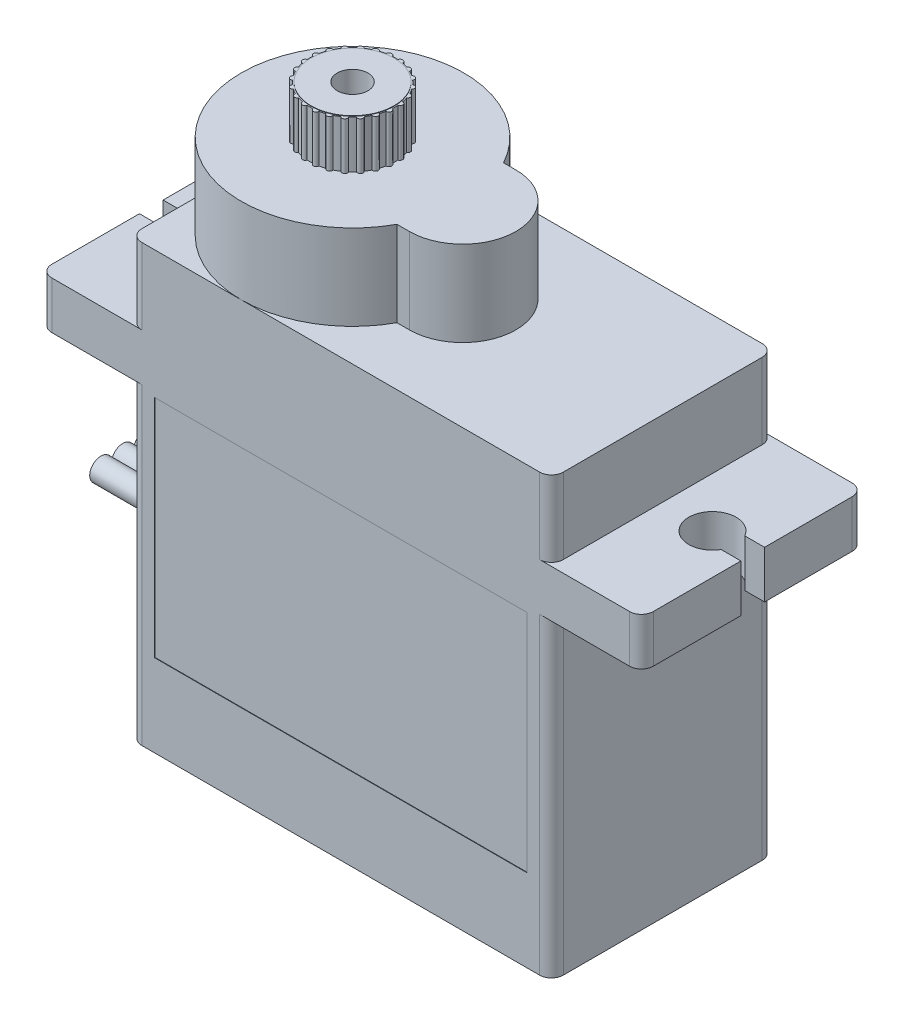
SolidWorks part; units mm, degrees
ref_plane "Front Plane" through (0, 0, 0) normal (0, 0, 1) x (1, 0, 0)
ref_plane "Top Plane" through (0, 0, 0) normal (0, 1, 0) x (1, 0, 0)
ref_plane "Right Plane" through (0, 0, 0) normal (1, 0, 0) x (0, 0, -1)
sketch "Sketch1" plane through (0, 0, 0) normal (0, 1, 0) x (1, 0, 0)
  line L1 (-11.303, -5.969) -> (11.303, -5.969)
  line L2 (-11.303, -5.969) -> (-11.303, 5.969)
  line L3 (-11.303, 5.969) -> (11.303, 5.969)
  line L4 (11.303, -5.969) -> (11.303, 5.969)
  line L5 (-11.303, -5.969) -> (11.303, 5.969) construction
  line L6 (-11.303, 5.969) -> (11.303, -5.969) construction
  point P0 (0, 0)
  dimension "D1" = 11.938
  dimension "D2" = 22.606
extrude "Boss-Extrude1" add sketch "Sketch1" along normal blind 23.368
sketch "Sketch3" plane through (0, 0, 0) normal (1, 0, 0) x (0, 0, -1)
  line L0 (-5.969, 23.368) -> (-5.969, 0) construction
  line L1 (-5.969, 16.764) -> (5.969, 16.764)
  line L2 (-5.969, 16.764) -> (-5.969, 19.304)
  line L3 (-5.969, 19.304) -> (5.969, 19.304)
  line L4 (5.969, 16.764) -> (5.969, 19.304)
  line L5 (5.969, 23.368) -> (5.969, 0) construction
  line L6 (-5.969, 0) -> (5.969, 0) construction
  dimension "D1" = 2.54
  dimension "D2" = 16.764
extrude "Boss-Extrude2" add sketch "Sketch3" along normal mid plane 32.258
sketch "Sketch4" plane through (0, 23.368, 0) normal (0, 1, 0) x (1, 0, 0)
  line L0 (-11.303, -5.969) -> (-11.303, 5.969) construction
  line L1 (-11.303, 0) -> (3.429, 0) construction
  line L2 (0.5715, 2.8575) -> (-0.0934, 2.8575)
  line L3 (0.5715, -2.8575) -> (-0.0934, -2.8575)
  arc A0 (-0.0934, 2.8575) -> (-0.0934, -2.8575) centre (-5.334, 0) ccw
  arc A1 (0.5715, -2.8575) -> (0.5715, 2.8575) centre (0.5715, 0) ccw
  dimension "D1" = 11.938
  dimension "D2" = 5.715
  dimension "D3" = 14.732
extrude "Boss-Extrude3" add sketch "Sketch4" along normal blind 4.572
sketch "Sketch5" plane through (0, 19.304, 0) normal (0, 1, 0) x (1, 0, 0)
  line L0 (16.129, 5.969) -> (16.129, -5.969) construction
  line L1 (16.129, 0.635) -> (16.129, -0.635)
  line L2 (16.129, 0) -> (12.7, 0) construction
  line L3 (16.129, 0.635) -> (15.0699, 0.635)
  line L4 (16.129, -0.635) -> (15.0699, -0.635)
  line L5 (0, 5.969) -> (0, -5.969) construction
  line L6 (11.303, 5.969) -> (-5.334, 5.969) construction
  line L7 (-5.334, -5.969) -> (11.303, -5.969) construction
  line L8 (16.129, 0.635) -> (15.0699, 0.635)
  line L9 (16.129, -0.635) -> (15.0699, -0.635)
  line L10 (-16.129, 0) -> (-12.7, 0) construction
  line L11 (-16.129, -0.635) -> (-15.0699, -0.635)
  line L12 (-16.129, 0.635) -> (-15.0699, 0.635)
  line L13 (-16.129, -0.635) -> (-15.0699, -0.635)
  line L14 (-16.129, 0.635) -> (-15.0699, 0.635)
  line L15 (-16.129, 0.635) -> (-16.129, -0.635)
  line L16 (-12.7, 0) -> (12.7, 0) construction
  arc A0 (15.0699, 0.635) -> (15.0699, -0.635) centre (13.97, 0) ccw
  arc A1 (-15.0699, 0.635) -> (-15.0699, -0.635) centre (-13.97, 0) cw
  point P2 (16.129, 0.635)
  point P3 (16.129, -0.635)
  point P12 (16.129, 0.635)
  point P22 (16.129, -0.635)
  point P31 (-16.129, -0.635)
  point P32 (-16.129, 0.635)
  point P33 (-16.129, -0.635)
  point P34 (-16.129, 0.635)
  line M8 (16.129, -5.969) -> (16.129, 5.969)
  dimension "D1" = 2.54
  dimension "D2" = 5.334
  dimension "D3" = 5.334
  dimension "D4" = 25.4
extrude "Cut-Extrude1" cut sketch "Sketch5" against normal through all both and the other way through all contours A1 L12 L15 L11 | L3 A0 L4 M8
sketch "Sketch6" plane through (0, 27.94, 0) normal (0, 1, 0) x (1, 0, 0)
  circle A0 centre (-5.334, 0) radius 2.413
  circle A1 centre (-5.334, 0) radius 2.286
  circle A2 centre (-5.334, 0) radius 0.8255
  dimension "D1" = 4.826
  dimension "D2" = 4.572
  dimension "D3" = 1.651
extrude "Boss-Extrude4" add sketch "Sketch6" along normal offset from surface (2.54 mm away) 30.48 contours A0 A1 | A1 A2 up to face at (0, 0, 0)
sketch "Sketch8" plane through (0, 30.48, 0) normal (0, 1, 0) x (1, 0, 0)
  line L0 (-5.334, 2.286) -> (-5.334, 2.413) construction
  line L1 (-5.334, 0) -> (-5.019, 2.3924) construction
  line L2 (-5.1845, 2.2811) -> (-5.334, 0) construction
  arc A0 (-5.019, 2.3924) -> (-5.1845, 2.2811) centre (-5.0387, 2.243) ccw
  circle A1 centre (-5.334, 0) radius 0.8255
  circle A2 centre (-5.334, 0) radius 0.8255 construction
  circle A3 centre (-5.334, 0) radius 2.286
  circle A4 centre (-5.334, 0) radius 2.286
  circle A5 centre (-5.334, 0) radius 2.413
  circle A6 centre (-5.334, 0) radius 2.413
  arc A7 (-5.649, 2.3924) -> (-5.4835, 2.2811) centre (-5.6293, 2.243) cw
  arc A8 (-5.019, 2.3924) -> (-4.888, 2.2421) centre (-5.0387, 2.243) cw
  arc A9 (-4.4106, 2.2293) -> (-4.5992, 2.1647) centre (-4.4683, 2.0901) ccw
  arc A10 (-4.4106, 2.2293) -> (-4.3229, 2.0503) centre (-4.4683, 2.0901) cw
  arc A11 (-3.8651, 1.9144) -> (-4.064, 1.9007) centre (-3.9568, 1.7948) ccw
  arc A12 (-3.8651, 1.9144) -> (-3.8267, 1.7187) centre (-3.9568, 1.7948) cw
  arc A13 (-3.4196, 1.4689) -> (-3.6153, 1.5073) centre (-3.5392, 1.3772) ccw
  arc A14 (-3.4196, 1.4689) -> (-3.4333, 1.27) centre (-3.5392, 1.3772) cw
  arc A15 (-3.1047, 0.9234) -> (-3.2837, 1.0111) centre (-3.2439, 0.8657) ccw
  arc A16 (-3.1047, 0.9234) -> (-3.1693, 0.7348) centre (-3.2439, 0.8657) cw
  arc A17 (-2.9416, 0.315) -> (-3.0919, 0.446) centre (-3.091, 0.2953) ccw
  arc A18 (-2.9416, 0.315) -> (-3.0529, 0.1495) centre (-3.091, 0.2953) cw
  arc A19 (-2.9416, -0.315) -> (-3.0529, -0.1495) centre (-3.091, -0.2953) ccw
  arc A20 (-2.9416, -0.315) -> (-3.0919, -0.446) centre (-3.091, -0.2953) cw
  arc A21 (-3.1047, -0.9234) -> (-3.1693, -0.7348) centre (-3.2439, -0.8657) ccw
  arc A22 (-3.1047, -0.9234) -> (-3.2837, -1.0111) centre (-3.2439, -0.8657) cw
  arc A23 (-3.4196, -1.4689) -> (-3.4333, -1.27) centre (-3.5392, -1.3772) ccw
  arc A24 (-3.4196, -1.4689) -> (-3.6153, -1.5073) centre (-3.5392, -1.3772) cw
  arc A25 (-3.8651, -1.9144) -> (-3.8267, -1.7187) centre (-3.9568, -1.7948) ccw
  arc A26 (-3.8651, -1.9144) -> (-4.064, -1.9007) centre (-3.9568, -1.7948) cw
  arc A27 (-4.4106, -2.2293) -> (-4.3229, -2.0503) centre (-4.4683, -2.0901) ccw
  arc A28 (-4.4106, -2.2293) -> (-4.5992, -2.1647) centre (-4.4683, -2.0901) cw
  arc A29 (-5.019, -2.3924) -> (-4.888, -2.2421) centre (-5.0387, -2.243) ccw
  arc A30 (-5.019, -2.3924) -> (-5.1845, -2.2811) centre (-5.0387, -2.243) cw
  arc A31 (-5.649, -2.3924) -> (-5.4835, -2.2811) centre (-5.6293, -2.243) ccw
  arc A32 (-5.649, -2.3924) -> (-5.78, -2.2421) centre (-5.6293, -2.243) cw
  arc A33 (-6.2574, -2.2293) -> (-6.0688, -2.1647) centre (-6.1997, -2.0901) ccw
  arc A34 (-6.2574, -2.2293) -> (-6.3451, -2.0503) centre (-6.1997, -2.0901) cw
  arc A35 (-6.8029, -1.9144) -> (-6.604, -1.9007) centre (-6.7112, -1.7948) ccw
  arc A36 (-6.8029, -1.9144) -> (-6.8413, -1.7187) centre (-6.7112, -1.7948) cw
  arc A37 (-7.2484, -1.4689) -> (-7.0527, -1.5073) centre (-7.1288, -1.3772) ccw
  arc A38 (-7.2484, -1.4689) -> (-7.2347, -1.27) centre (-7.1288, -1.3772) cw
  arc A39 (-7.5633, -0.9234) -> (-7.3843, -1.0111) centre (-7.4241, -0.8657) ccw
  arc A40 (-7.5633, -0.9234) -> (-7.4987, -0.7348) centre (-7.4241, -0.8657) cw
  arc A41 (-7.7264, -0.315) -> (-7.5761, -0.446) centre (-7.577, -0.2953) ccw
  arc A42 (-7.7264, -0.315) -> (-7.6151, -0.1495) centre (-7.577, -0.2953) cw
  arc A43 (-7.7264, 0.315) -> (-7.6151, 0.1495) centre (-7.577, 0.2953) ccw
  arc A44 (-7.7264, 0.315) -> (-7.5761, 0.446) centre (-7.577, 0.2953) cw
  arc A45 (-7.5633, 0.9234) -> (-7.4987, 0.7348) centre (-7.4241, 0.8657) ccw
  arc A46 (-7.5633, 0.9234) -> (-7.3843, 1.0111) centre (-7.4241, 0.8657) cw
  arc A47 (-7.2484, 1.4689) -> (-7.2347, 1.27) centre (-7.1288, 1.3772) ccw
  arc A48 (-7.2484, 1.4689) -> (-7.0527, 1.5073) centre (-7.1288, 1.3772) cw
  arc A49 (-6.8029, 1.9144) -> (-6.8413, 1.7187) centre (-6.7112, 1.7948) ccw
  arc A50 (-6.8029, 1.9144) -> (-6.604, 1.9007) centre (-6.7112, 1.7948) cw
  arc A51 (-6.2574, 2.2293) -> (-6.3451, 2.0503) centre (-6.1997, 2.0901) ccw
  arc A52 (-6.2574, 2.2293) -> (-6.0688, 2.1647) centre (-6.1997, 2.0901) cw
  arc A53 (-5.649, 2.3924) -> (-5.78, 2.2421) centre (-5.6293, 2.243) ccw
  point P157 (-5.334, 0)
  circle M8 centre (-5.334, 0) radius 2.413
  dimension "D4" = 7.5
  dimension "D5" = 3.75
  dimension "D1" = 0
  dimension "D2" = 0
  dimension "D3" = 0
  dimension "D6" = 24
extrude "Cut-Extrude2" cut sketch "Sketch8" against normal up to surface (2.54 mm away) contours A49 A48 A4 M8 | A47 A46 A4 M8 | A45 A44 A4 M8 | A43 A42 A4 M8 | A41 A40 A4 M8 | A39 A38 A4 M8 | A37 A36 A4 M8 | A35 A34 A4 M8 | A33 A32 A4 M8 | A31 A30 A4 M8 | A29 A28 A4 M8 | A27 A26 A4 M8 | A25 A24 A4 M8 | A23 A22 A4 M8 | A21 A20 A4 M8 | A19 A18 A4 M8 | A17 A16 A4 M8 | A15 A14 A4 M8 | A13 A12 A4 M8 | A11 A10 A4 M8 | A9 A8 A4 M8 | A7 A4 A0 M8 | A53 A6 A52 A4 | A51 A50 A4 M8 up to face at (-5.334, 27.94, 2.413)
sketch "Sketch9" plane through (0, 30.48, 0) normal (0, 1, 0) x (1, 0, 0)
  circle A0 centre (-5.334, 0) radius 2.2225
  circle A1 centre (-5.334, 0) radius 0.8255
  circle A2 centre (-5.334, 0) radius 0.8255
  dimension "D2" = 4.445
  dimension "D1" = 0
extrude "Boss-Extrude5" add sketch "Sketch9" along normal blind 0.0254
fillet "Fillet1" radius 0.635 8 edges at (-11.303, 8.382, -5.969) (-11.303, 21.336, -5.969) (-11.303, 21.336, 5.969) (-11.303, 8.382, 5.969) (11.303, 8.382, -5.969) (11.303, 8.382, 5.969) (11.303, 21.336, -5.969) (11.303, 21.336, 5.969)
fillet "Fillet2" radius 0.635 4 edges at (-16.129, 18.034, -5.969) (16.129, 18.034, -5.969) (16.129, 18.034, 5.969) (-16.129, 18.034, 5.969)
sketch "Sketch10" plane through (0, 0, 0) normal (0, -1, 0) x (1, 0, 0)
  line L0 (-10.668, 5.969) -> (10.668, 5.969) construction
  line L1 (-11.303, -5.334) -> (-11.303, 5.334) construction
  line L2 (-11.303, 0) -> (11.303, 0) construction
  line L3 (11.303, 5.334) -> (11.303, -5.334) construction
  line L5 (0, 5.969) -> (0, -5.969) construction
  line L6 (10.668, -5.969) -> (-10.668, -5.969) construction
  circle A0 centre (-10.16, 4.826) radius 0.9842
  circle A1 centre (-10.16, -4.826) radius 0.9842
  circle A2 centre (10.16, -4.826) radius 0.9842
  circle A3 centre (10.16, 4.826) radius 0.9842
  dimension "D1" = 1.9685
  dimension "D2" = 1.143
  dimension "D3" = 1.143
extrude "Cut-Extrude3" cut sketch "Sketch10" against normal blind 2.54
sketch "Sketch11" plane through (-11.303, 0, 0) normal (-1, 0, 0) x (0, 0, 1)
  line L0 (-1.778, 6.35) -> (1.778, 6.35)
  line L1 (0, 0) -> (0, 6.35) construction
  line L2 (-5.334, 0) -> (5.334, 0) construction
  line L3 (-1.778, 6.35) -> (-1.778, 7.5565)
  line L4 (-1.778, 7.5565) -> (1.778, 7.5565)
  line L5 (1.778, 7.5565) -> (1.778, 6.35)
  circle A0 centre (-1.1747, 6.9532) radius 0.6033
  circle A1 centre (0, 6.9532) radius 0.6033
  circle A2 centre (1.1747, 6.9532) radius 0.6033
  point P10 (0, 6.9532)
  point P15 (0, 0)
  point P16 (0, 0)
  point P17 (0, 0)
  dimension "D1" = 6.35
  dimension "D2" = 3.556
  dimension "D3" = 1.2065
extrude "Boss-Extrude7" add sketch "Sketch11" along normal blind 6.35 contours A1 A0 | A2 A1 A0 | A2 A1 | A0 A1 | A1 A2
sketch "Sketch13" plane through (0, 0, 5.969) normal (0, 0, 1) x (1, 0, 0)
  line L0 (-10.668, 0) -> (10.668, 0) construction
  line L1 (-9.9949, 4.4196) -> (9.9949, 4.4196)
  line L2 (-9.9949, 4.4196) -> (-9.9949, 16.51)
  line L3 (-9.9949, 16.51) -> (9.9949, 16.51)
  line L4 (9.9949, 4.4196) -> (9.9949, 16.51)
  line L5 (-9.9949, 4.4196) -> (9.9949, 16.51) construction
  line L6 (-9.9949, 16.51) -> (9.9949, 4.4196) construction
  point P0 (0, 10.4648)
  point P5 (0.3806, 8.8907)
  point P8 (0, 0)
  dimension "D1" = 12.0904
  dimension "D2" = 16.51
  dimension "D3" = 19.9898
extrude "Cut-Extrude4" cut sketch "Sketch13" against normal blind 0.0254
